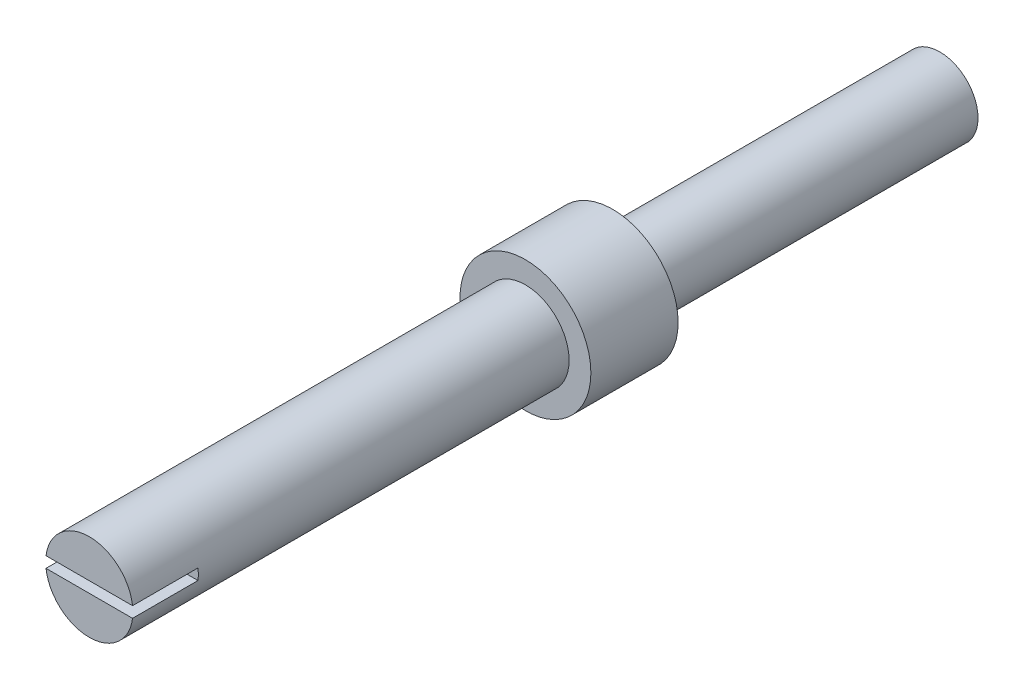
SolidWorks part; units mm, degrees
ref_plane "Front Plane" through (0, 0, 0) normal (0, 0, 1) x (1, 0, 0)
ref_plane "Top Plane" through (0, 0, 0) normal (0, 1, 0) x (1, 0, 0)
ref_plane "Right Plane" through (0, 0, 0) normal (1, 0, 0) x (0, 0, -1)
sketch "스케치1" plane through (0, 0, 0) normal (0, 0, 1) x (1, 0, 0)
  circle A0 centre (0, 0) radius 3
extrude "보스-돌출1" add sketch "스케치1" along normal blind 4
sketch "스케치2" plane through (0, 0, 4) normal (0, 0, 1) x (1, 0, 0)
  circle A0 centre (0, 0) radius 2
extrude "보스-돌출2" add sketch "스케치2" along normal blind 20
sketch "스케치3" plane through (0, 0, 0) normal (0, 0, -1) x (-1, 0, 0)
  circle A0 centre (0, 0) radius 1.75
extrude "보스-돌출3" add sketch "스케치3" along normal blind 15
sketch "스케치4" plane through (0, 0, 24) normal (0, 0, 1) x (1, 0, 0)
  line L0 (0, 0) -> (50000, 0) construction
  line L2 (-2.2422, 0.25) -> (2.219, 0.25)
  line L3 (-2.2422, 0.25) -> (-2.2422, -0.25)
  line L4 (-2.2422, -0.25) -> (2.219, -0.25)
  line L5 (2.219, 0.25) -> (2.219, -0.25)
  dimension "D1" = 0.5
  dimension "D2" = 0.25
extrude "컷-돌출1" cut sketch "스케치4" against normal blind 3
